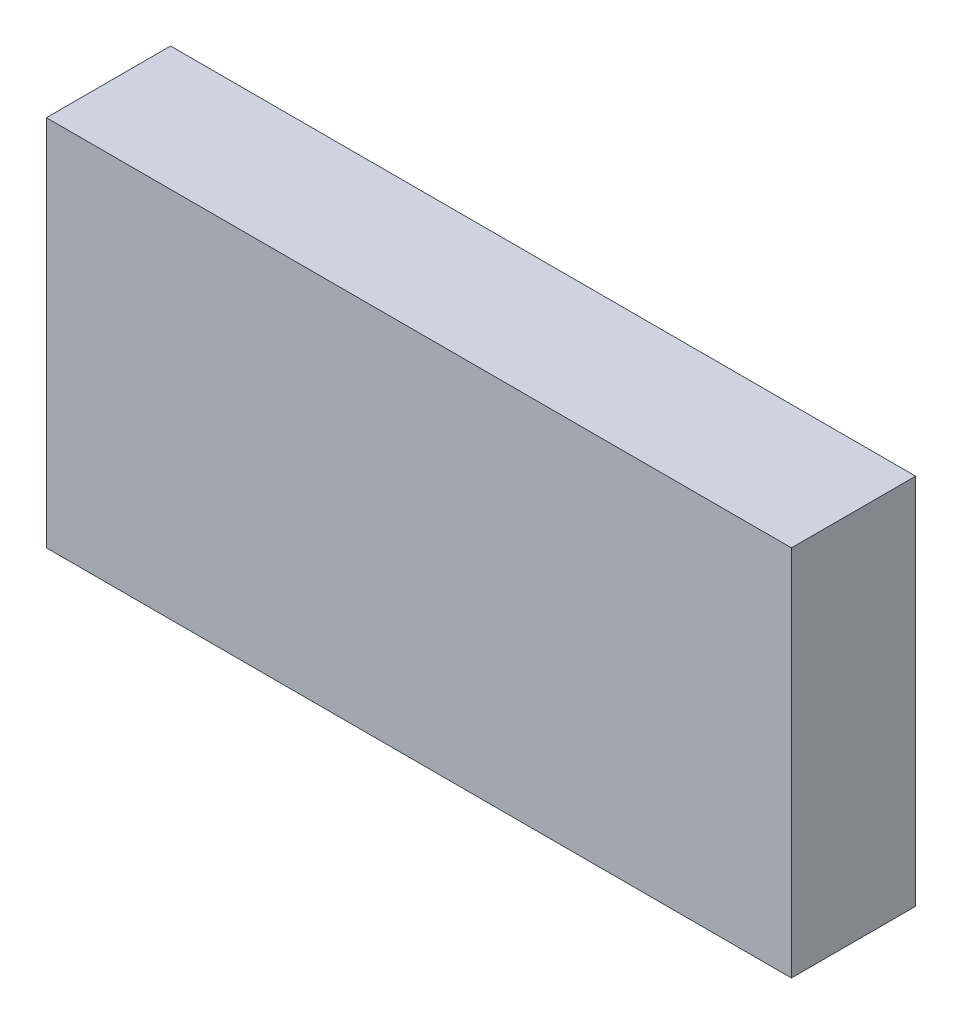
SolidWorks part; units mm, degrees
ref_plane "Front Plane" through (0, 0, 0) normal (0, 0, 1) x (1, 0, 0)
ref_plane "Top Plane" through (0, 0, 0) normal (0, 1, 0) x (1, 0, 0)
ref_plane "Right Plane" through (0, 0, 0) normal (1, 0, 0) x (0, 0, -1)
sketch "Sketch1" plane through (0, 0, 0) normal (0, 0, 1) x (1, 0, 0)
  line L1 (3000, -1500) -> (-3000, -1500)
  line L2 (3000, -1500) -> (3000, 1500)
  line L3 (3000, 1500) -> (-3000, 1500)
  line L4 (-3000, -1500) -> (-3000, 1500)
  line L5 (3000, -1500) -> (-3000, 1500) construction
  line L6 (3000, 1500) -> (-3000, -1500) construction
  point P0 (0, 0)
  dimension "D1" = 3000
  dimension "D2" = 6000
extrude "Boss-Extrude1" add sketch "Sketch1" along normal blind 1000 contours L2 L3 L4 L1
